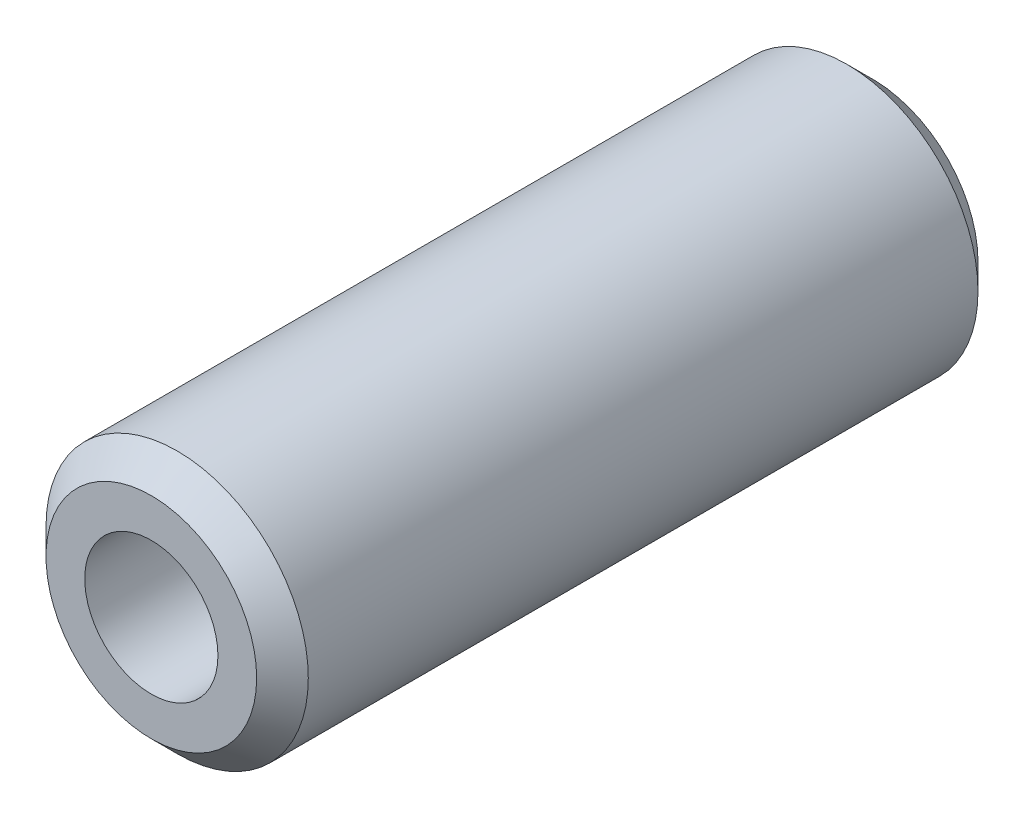
SolidWorks part; units mm, degrees
ref_plane "Front Plane" through (0, 0, 0) normal (0, 0, 1) x (1, 0, 0)
ref_plane "Top Plane" through (0, 0, 0) normal (0, 1, 0) x (1, 0, 0)
ref_plane "Right Plane" through (0, 0, 0) normal (1, 0, 0) x (0, 0, -1)
sketch "Sketch2" plane through (0, 0, 0) normal (0, 0, 1) x (1, 0, 0)
  circle A0 centre (0, 0) radius 12.7
  dimension "D1" = 25.4
extrude "Boss-Extrude1" add sketch "Sketch2" along normal blind 69.85
sketch "Sketch3" plane through (0, 0, 69.85) normal (0, 0, 1) x (1, 0, 0)
  circle A0 centre (0, 0) radius 6.45
  dimension "D1" = 12.9
extrude "Cut-Extrude1" cut sketch "Sketch3" against normal through all contours A0
chamfer "Chamfer1" distance 2.5 angle 45 2 edges at (12.7, 0, 0) (12.7, 0, 69.85)
